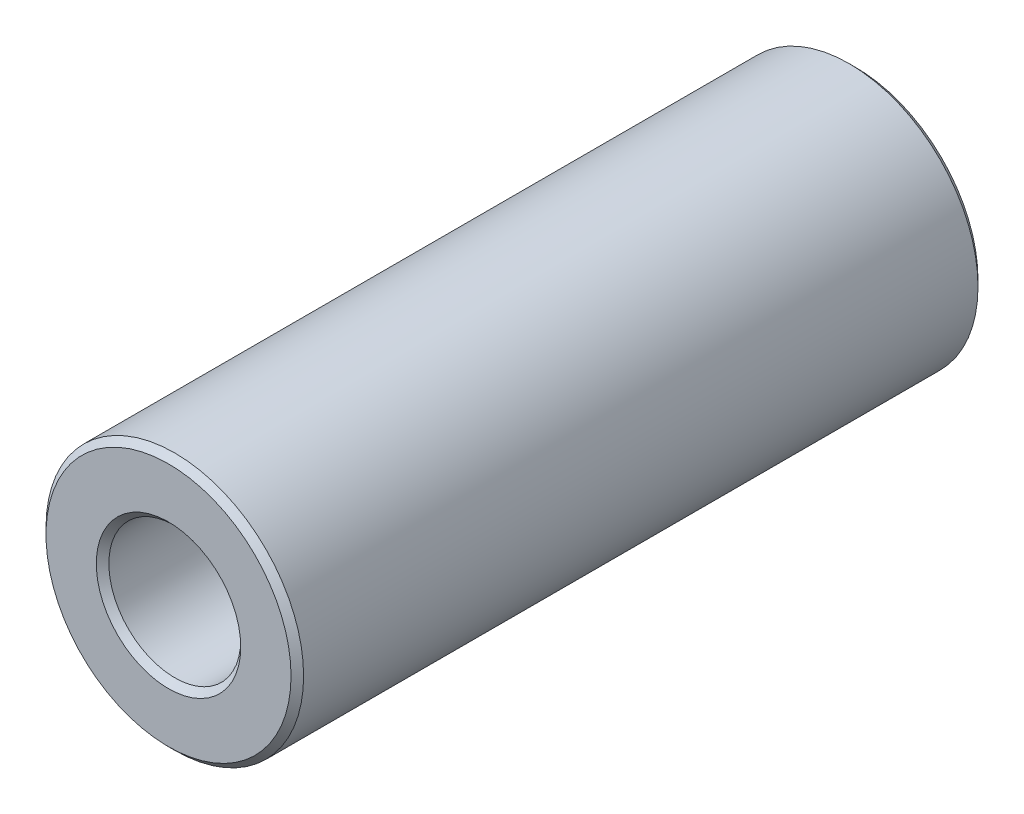
SolidWorks part; units mm, degrees
ref_plane "Front Plane" through (0, 0, 0) normal (0, 0, 1) x (1, 0, 0)
ref_plane "Top Plane" through (0, 0, 0) normal (0, 1, 0) x (1, 0, 0)
ref_plane "Right Plane" through (0, 0, 0) normal (1, 0, 0) x (0, 0, -1)
sketch "Sketch1" plane through (0, 0, 0) normal (0, 0, 1) x (1, 0, 0)
  circle A0 centre (0, 0) radius 4.7625 construction
  circle A1 centre (0, 0) radius 2.4384 construction
  point P4 (0, 4.7625)
  dimension "ID" = 4.8768
  dimension "OD" = 9.525
sketch "Sketch2" plane through (0, 0, 0) normal (1, 0, 0) x (0, 0, -1)
  line L0 (-12.7, 4.7625) -> (12.7, 4.7625) construction
  dimension "Length" = 25.4
sketch "Sketch3" plane through (0, 0, 0) normal (0, 0, 1) x (1, 0, 0)
  circle A0 centre (0, 0) radius 2.4384 construction
  circle A1 centre (0, 0) radius 4.7625 construction
  circle A2 centre (0, 0) radius 2.4384
  circle A3 centre (0, 0) radius 4.7625
extrude "Boss-Extrude1" add sketch "Sketch3" against normal up to vertex (12.7 mm away) and the other way up to vertex (12.7 mm away) up to point (0, 4.7625, -12.7) other way up to point (0, 4.7625, 12.7)
chamfer "Chamfer1" distance 0.2324 angle 45 4 edges at (4.7625, 0, 12.7) (4.7625, 0, -12.7) (2.4384, 0, 12.7) (2.4384, 0, -12.7)
equation "\"D1@Chamfer1\"=(\"OD@Sketch1\"-\"ID@Sketch1\")*0.05"
